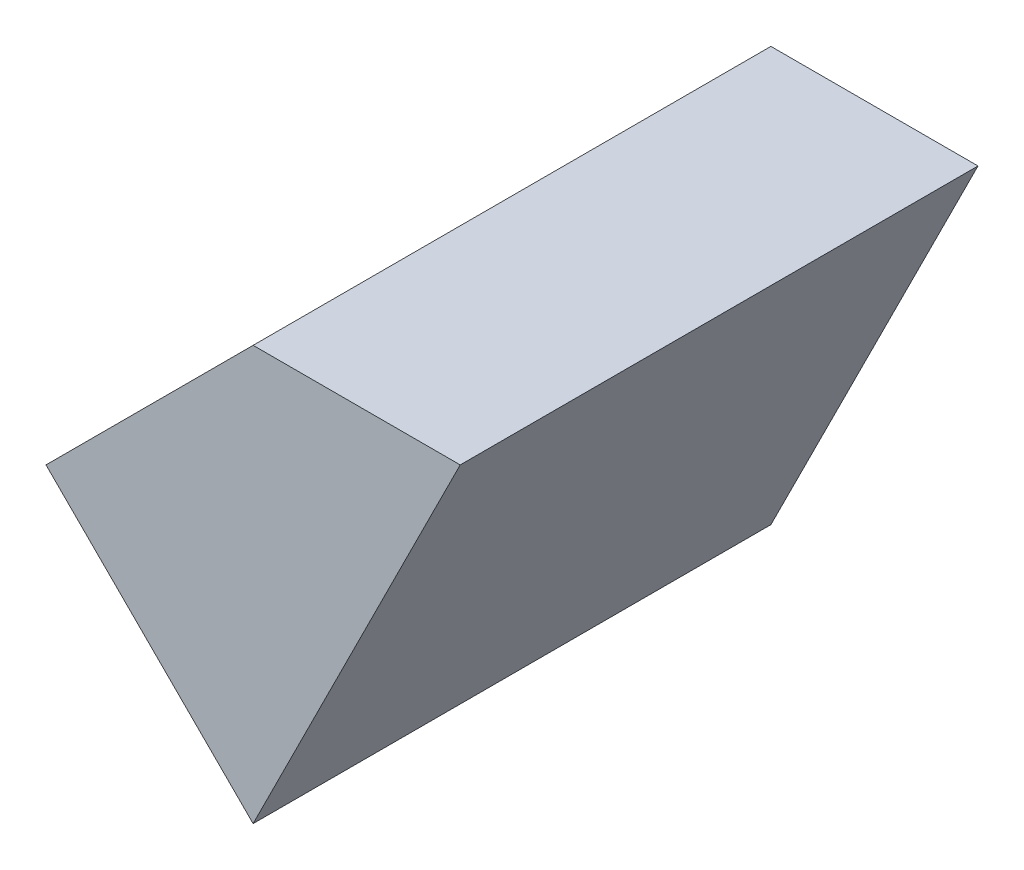
SolidWorks part; units mm, degrees
ref_plane "Front Plane" through (0, 0, 0) normal (0, 0, 1) x (1, 0, 0)
ref_plane "Top Plane" through (0, 0, 0) normal (0, 1, 0) x (1, 0, 0)
ref_plane "Right Plane" through (0, 0, 0) normal (1, 0, 0) x (0, 0, -1)
sketch "Sketch1" plane through (0, 0, 0) normal (0, 0, 1) x (1, 0, 0)
  line L0 (0, 0) -> (10, 0)
  line L1 (10, 0) -> (0, -20)
  line L2 (0, -20) -> (-10, -10)
  line L3 (-10, -10) -> (0, 0)
  point P3 (0, -10)
  point P5 (-10, -20)
  point P6 (10, -20)
  dimension "D1" = 10
  dimension "D2" = 10
  dimension "D3" = 20
  dimension "D4" = 10
  dimension "D5" = 10
  dimension "D6" = 10
  dimension "D7" = 20
extrude "Boss-Extrude1" add sketch "Sketch1" along normal blind 25
